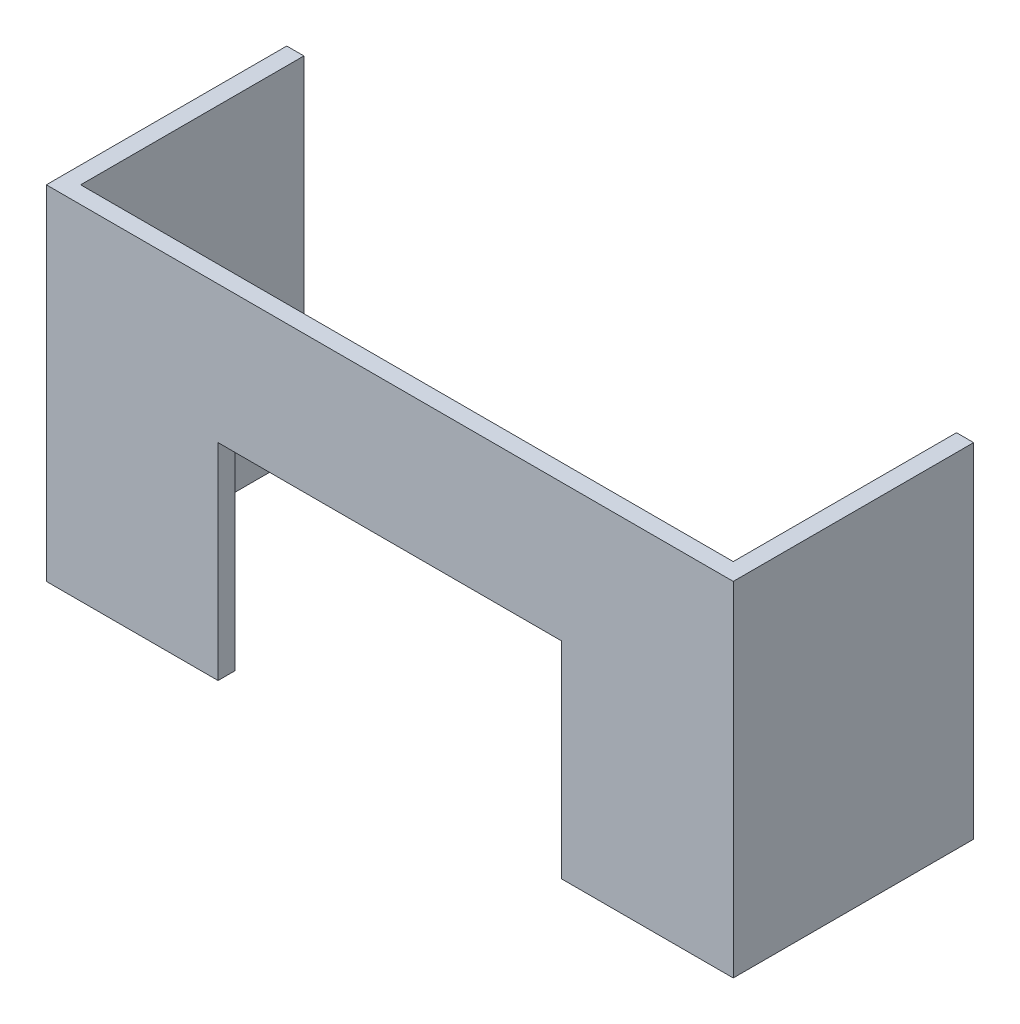
SolidWorks part; units mm, degrees
ref_plane "Front Plane" through (0, 0, 0) normal (0, 0, 1) x (1, 0, 0)
ref_plane "Top Plane" through (0, 0, 0) normal (0, 1, 0) x (1, 0, 0)
ref_plane "Right Plane" through (0, 0, 0) normal (1, 0, 0) x (0, 0, -1)
sketch "Sketch1" plane through (0, 0, 0) normal (0, 1, 0) x (1, 0, 0)
  line L1 (-200, 75) -> (200, 75)
  line L2 (-200, 75) -> (-200, -75)
  line L3 (-200, -75) -> (200, -75)
  line L4 (200, 75) -> (200, -75)
  line L5 (-200, 75) -> (200, -75) construction
  line L6 (-200, -75) -> (200, 75) construction
  point P0 (0, 0)
  dimension "D1" = 400
  dimension "D2" = 150
extrude "Boss-Extrude1" add sketch "Sketch1" along normal blind 200
sketch "Sketch2" plane through (0, 200, 0) normal (0, 1, 0) x (1, 0, 0)
  line L0 (200, 75) -> (-200, 75) construction
  line L1 (-190, 65) -> (190, 65)
  line L2 (-190, 65) -> (-190, -65)
  line L3 (-190, -65) -> (190, -65)
  line L4 (190, 65) -> (190, -65)
  line L5 (-190, 65) -> (190, -65) construction
  line L6 (-190, -65) -> (190, 65) construction
  line L7 (200, -75) -> (200, 75) construction
  point P0 (0, 0)
  dimension "D1" = 10
  dimension "D2" = 10
extrude "Cut-Extrude1" cut sketch "Sketch2" against normal blind 200
sketch "Sketch3" plane through (0, 0, 75) normal (0, 0, 1) x (1, 0, 0)
  line L0 (-200, 0) -> (200, 0) construction
  line L1 (-100, 120) -> (100, 120)
  line L2 (-100, 120) -> (-100, 0)
  line L3 (-100, 0) -> (100, 0)
  line L4 (100, 120) -> (100, 0)
  point P7 (0, 0)
  dimension "D1" = 200
  dimension "D2" = 120
extrude "Cut-Extrude2" cut sketch "Sketch3" against normal blind 20
sketch "Sketch4" plane through (0, 0, -75) normal (0, 0, -1) x (-1, 0, 0)
  line L1 (-200, 200) -> (200, 200)
  line L2 (-200, 200) -> (-200, 0)
  line L3 (-200, 0) -> (200, 0)
  line L4 (200, 200) -> (200, 0)
extrude "Cut-Extrude3" cut sketch "Sketch4" against normal up to vertex (10 mm away) up to point (190, 200, -65)
